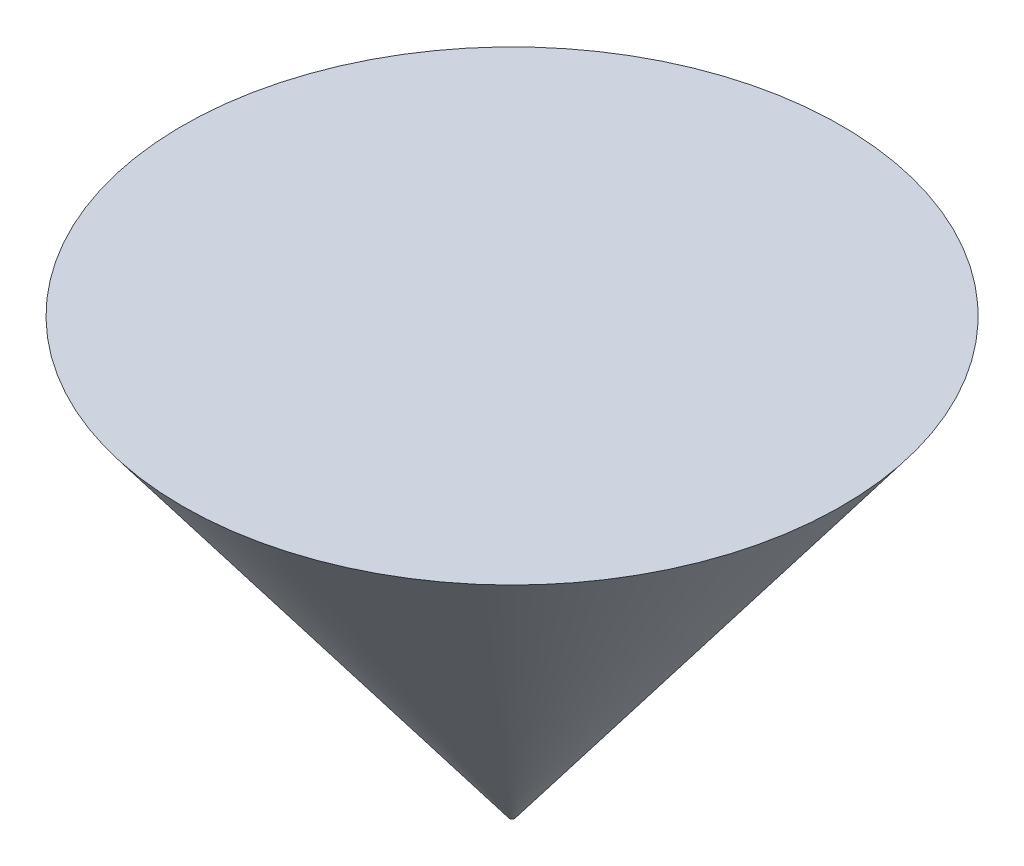
SolidWorks part; units mm, degrees
material "Air"
ref_plane "Front Plane" through (0, 0, 0) normal (0, 0, 1) x (1, 0, 0)
ref_plane "Top Plane" through (0, 0, 0) normal (0, 1, 0) x (1, 0, 0)
ref_plane "Right Plane" through (0, 0, 0) normal (1, 0, 0) x (0, 0, -1)
sketch "Sketch1" plane through (0, 0, 0) normal (0, 1, 0) x (1, 0, 0)
  circle A0 centre (0, 0) radius 12.7
extrude "Boss-Extrude1" add sketch "Sketch1" along normal blind 2000 draft 37 draft outward yes
